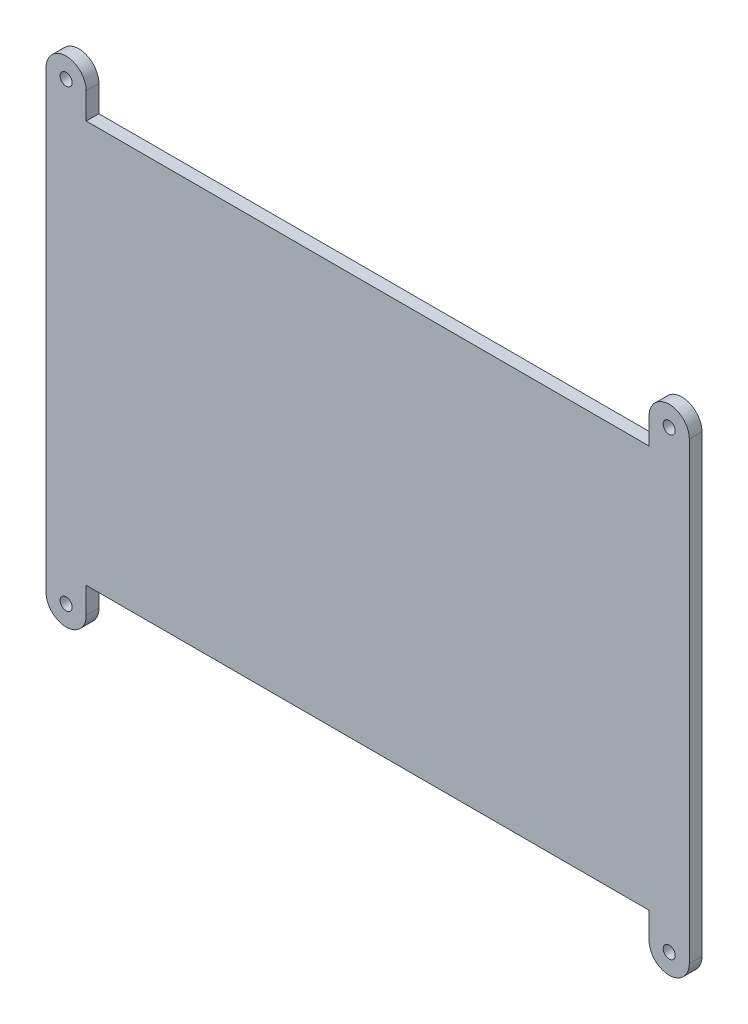
SolidWorks part; units mm, degrees
ref_plane "Front Plane" through (0, 0, 0) normal (0, 0, 1) x (1, 0, 0)
ref_plane "Top Plane" through (0, 0, 0) normal (0, 1, 0) x (1, 0, 0)
ref_plane "Right Plane" through (0, 0, 0) normal (1, 0, 0) x (0, 0, -1)
sketch "Sketch1" plane through (0, 0, 0) normal (0, 0, 1) x (1, 0, 0)
  line L0 (0, 53.8813) -> (0, -54.0479) construction
  line L1 (-74.9508, 0) -> (100.2675, 0) construction
  line L2 (-35.56, 25.4) -> (35.56, 25.4)
  line L3 (35.56, 25.4) -> (35.56, 28.702)
  line L4 (40.64, 28.702) -> (40.64, -28.702)
  line L5 (35.56, -25.4) -> (35.56, -28.702)
  line L6 (-35.56, -25.4) -> (35.56, -25.4)
  line L7 (-35.56, -25.4) -> (-35.56, -28.702)
  line L8 (-40.64, 28.702) -> (-40.64, -28.702)
  line L9 (-35.56, 25.4) -> (-35.56, 28.702)
  arc A0 (40.64, 28.702) -> (35.56, 28.702) centre (38.1, 28.702) ccw
  arc A1 (40.64, -28.702) -> (35.56, -28.702) centre (38.1, -28.702) cw
  arc A2 (-40.64, -28.702) -> (-35.56, -28.702) centre (-38.1, -28.702) ccw
  arc A3 (-40.64, 28.702) -> (-35.56, 28.702) centre (-38.1, 28.702) cw
  point P5 (-40.64, 0)
  point P14 (40.64, 0)
  point P23 (0, -25.4)
  point P24 (0, 25.4)
  point P25 (38.1, 31.242)
  point P26 (38.1, -31.242)
  dimension "D1" = 81.28
  dimension "D2" = 50.8
  dimension "D3" = 62.484
  dimension "D4" = 76.2
extrude "Boss-Extrude1" add sketch "Sketch1" along normal blind 1.6 contours L8 A2 L7 L6 L5 A1 L4 A0 L3 L2 L9 A3
sketch "Sketch2" plane through (0, 0, 1.6) normal (0, 0, 1) x (1, 0, 0)
  line L0 (0, 32.1045) -> (0, -31.9375) construction
  line L1 (-45.2552, 0) -> (45.9232, 0) construction
  line L2 (38.1, 31.242) -> (38.1, 39.1848) construction
  line L3 (35.56, 28.702) -> (40.64, 28.702) construction
  circle A0 centre (38.1, 28.702) radius 0.762
  arc A1 (40.64, 28.702) -> (35.56, 28.702) centre (38.1, 28.702) ccw construction
  circle A2 centre (-38.1, 28.702) radius 0.762
  circle A3 centre (38.1, -28.702) radius 0.762
  circle A4 centre (-38.1, -28.702) radius 0.762
  point P20 (0, 0)
  dimension "D1" = 1.524
extrude "Cut-Extrude1" cut sketch "Sketch2" against normal through all
